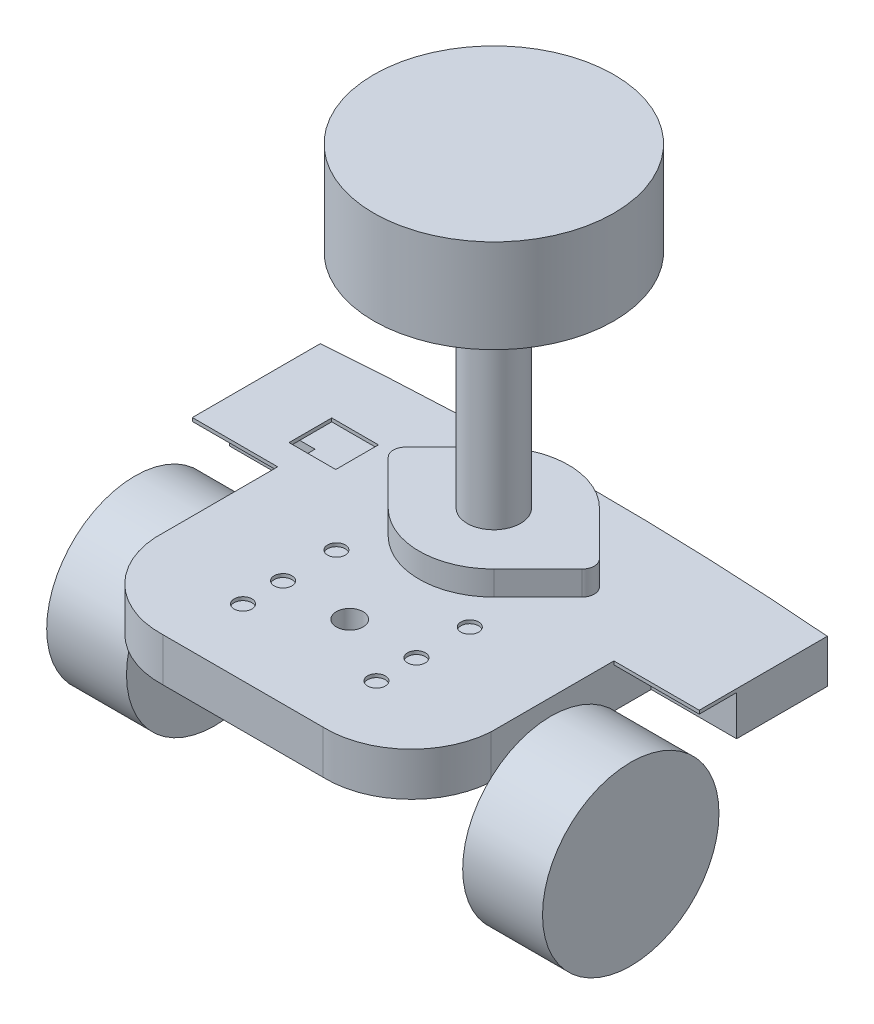
SolidWorks part; units mm, degrees
ref_plane "Front Plane" through (0, 0, 0) normal (0, 0, 1) x (1, 0, 0)
ref_plane "Top Plane" through (0, 0, 0) normal (0, 1, 0) x (1, 0, 0)
ref_plane "Right Plane" through (0, 0, 0) normal (1, 0, 0) x (0, 0, -1)
sketch "Sketch1" plane through (0, 0, 0) normal (0, 1, 0) x (1, 0, 0)
  line L0 (0, 0) -> (0, 125.2845) construction
  line L1 (19.05, 0) -> (-19.05, 0)
  line L2 (-40.005, 19.05) -> (-40.005, 48.26)
  line L3 (-40.005, 48.26) -> (-60.325, 48.26)
  line L4 (-60.325, 48.26) -> (-60.325, 78.74)
  line L5 (-60.325, 78.74) -> (60.325, 78.74)
  line L6 (60.325, 48.26) -> (60.325, 78.74)
  line L7 (40.005, 48.26) -> (60.325, 48.26)
  line L8 (40.005, 19.05) -> (40.005, 48.26)
  arc A0 (-40.005, 19.05) -> (-19.05, 0) centre (-19.724, 20.3088) ccw
  arc A1 (40.005, 19.05) -> (19.05, 0) centre (19.724, 20.3088) cw
  point P14 (0, 78.74)
  dimension "D4" = 20.32
  dimension "D1" = 120.65
  dimension "D2" = 80.01
  dimension "D3" = 38.1
  dimension "D5" = 19.05
  dimension "D6" = 48.26
  dimension "D7" = 78.74
extrude "Extrude1" add sketch "Sketch1" along normal blind 0.8128
sketch "Sketch3" plane through (0, 0.8128, 0) normal (0, 1, 0) x (-1, 0, 0)
  line L0 (0, -78.74) -> (0, 0) construction
  line L1 (-60.325, -78.74) -> (60.325, -78.74) construction
  line L2 (-21, -59.69) -> (21, -59.69) construction
  circle A0 centre (0, -59.69) radius 17.78
  circle A1 centre (21, -59.69) radius 1.651
  circle A2 centre (-21, -59.69) radius 1.651
  dimension "D1" = 35.56
  dimension "D3" = 42
  dimension "D4" = 3.302
  dimension "D2" = 19.05
extrude "Extrude2" cut sketch "Sketch3" against normal through all
sketch "Sketch4" plane through (0, 0.8128, 0) normal (0, 1, 0) x (-1, 0, 0)
  line L0 (38.1, -78.74) -> (38.1, -47.0431) construction
  line L1 (-60.325, -78.74) -> (60.325, -78.74) construction
  line L2 (60.325, -78.74) -> (60.325, -48.26) construction
  line L3 (38.1, -59.69) -> (21, -59.69) construction
  line L4 (43.6562, -54.61) -> (32.5438, -54.61)
  line L5 (43.6562, -54.61) -> (43.6562, -64.77)
  line L6 (43.6562, -64.77) -> (32.5438, -64.77)
  line L7 (32.5438, -54.61) -> (32.5438, -64.77)
  line L8 (43.6562, -54.61) -> (32.5438, -64.77) construction
  line L9 (43.6562, -64.77) -> (32.5438, -54.61) construction
  point P6 (38.1, -59.69)
  dimension "D1" = 22.225
  dimension "D2" = 11.1125
  dimension "D3" = 10.16
extrude "Cut-Extrude1" cut sketch "Sketch4" against normal through all
sketch "Sketch5" plane through (0, 0.8128, 0) normal (0, 1, 0) x (-1, 0, 0)
  line L0 (15.875, -78.74) -> (15.875, 0) construction
  line L1 (0, -78.74) -> (0, 0) construction
  line L2 (-60.325, -78.74) -> (60.325, -78.74) construction
  line L3 (19.05, 0) -> (-19.05, 0) construction
  circle A0 centre (15.875, -38.1) radius 2.1082
  circle A1 centre (15.875, -25.4) radius 2.1082
  circle A2 centre (15.875, -15.875) radius 2.1082
  circle A3 centre (-15.875, -15.875) radius 2.1082
  circle A4 centre (-15.875, -25.4) radius 2.1082
  circle A5 centre (-15.875, -38.1) radius 2.1082
  dimension "D2" = 4.2164
  dimension "D3" = 12.7
  dimension "D4" = 9.525
  dimension "D5" = 15.875
  dimension "D1" = 15.875
extrude "Extrude3" cut sketch "Sketch5" against normal through all
sketch "Sketch6" plane through (0, 0.8128, 0) normal (0, 1, 0) x (1, 0, 0)
  line L0 (-60.325, 78.74) -> (60.325, 78.74)
  arc A0 (-60.325, 78.74) -> (60.325, 78.74) centre (0, -680.8684) cw
  dimension "D1" = 762
extrude "Extrude5" add sketch "Sketch6" against normal through all
sketch "Sketch7" plane through (0, 0, 0) normal (0, -1, 0) x (1, 0, 0)
  line L7 (-60.325, -78.74) -> (-60.325, -57.15)
  line L8 (-60.325, -78.74) -> (-60.325, -48.26) construction
  line L9 (-60.325, -57.15) -> (-40.005, -57.15)
  line L10 (-60.325, -48.26) -> (-40.005, -48.26) construction
  line L11 (0, -81.1316) -> (0, 0) construction
  line L12 (60.325, -57.15) -> (40.005, -57.15)
  line L13 (60.325, -78.74) -> (60.325, -57.15)
  line L14 (-40.005, -19.05) -> (-40.005, -48.26)
  line L15 (-40.005, -48.26) -> (-60.325, -48.26)
  line L16 (-60.325, -48.26) -> (-60.325, -78.74)
  line L17 (60.325, -78.74) -> (60.325, -48.26)
  line L18 (60.325, -48.26) -> (40.005, -48.26)
  line L19 (40.005, -48.26) -> (40.005, -19.05)
  line L20 (19.05, 0) -> (-19.05, 0)
  line L21 (-40.005, -19.05) -> (-40.005, -57.15)
  line L26 (40.005, -57.15) -> (40.005, -19.05)
  line L27 (19.05, 0) -> (-19.05, 0)
  arc A6 (-19.05, 0) -> (-40.005, -19.05) centre (-19.724, -20.3088) ccw
  arc A7 (-60.325, -78.74) -> (60.325, -78.74) centre (0, 680.8684) ccw
  arc A8 (40.005, -19.05) -> (19.05, 0) centre (19.724, -20.3088) ccw
  arc A9 (-19.05, 0) -> (-40.005, -19.05) centre (-19.724, -20.3088) ccw
  arc A10 (-60.325, -78.74) -> (60.325, -78.74) centre (0, 680.8684) ccw
  arc A11 (40.005, -19.05) -> (19.05, 0) centre (19.724, -20.3088) ccw
  dimension "D2" = 8.89
  dimension "D1" = 0
extrude "Extrude6" add sketch "Sketch7" along normal blind 9.525
sketch "Sketch8" plane through (0, 0, 0) normal (0, 1, 0) x (1, 0, 0)
  line L0 (-23.0656, 61.7523) -> (-12.5824, 72.2523)
  line L1 (-21, 59.69) -> (0, 59.69) construction
  line L2 (0, 59.69) -> (0, 77.47) construction
  line L3 (23.0656, 61.7523) -> (12.5824, 72.2523)
  line L4 (-23.0656, 57.6277) -> (-12.5824, 47.1277)
  line L5 (23.0656, 57.6277) -> (12.5824, 47.1277)
  circle A0 centre (0, 59.69) radius 17.78
  circle A1 centre (21, 59.69) radius 2.9188
  circle A2 centre (-21, 59.69) radius 2.9188
  circle A3 centre (0, 59.69) radius 17.78 construction
  circle M1 centre (0, 59.69) radius 17.78
extrude "Extrude7" add sketch "Sketch8" along normal blind 6.604 contours A2 L4 L0 M1 | A2 | M1 | A1 L3 L5 M1 | A1
sketch "Sketch9" plane through (40.005, 0, 0) normal (1, 0, 0) x (0, 0, -1)
  line L0 (0, 0.8128) -> (0, -9.525) construction
  line L1 (19.05, 0.8128) -> (48.26, 0.8128) construction
  circle A0 centre (33.274, -24.0792) radius 21
  point P2 (0, -4.3561)
  dimension "D1" = 42
  dimension "D2" = 33.274
  dimension "D3" = 24.892
extrude "Extrude8" add sketch "Sketch9" along normal blind 19 separate body
mirror "Mirror3" about plane through (0, 0, 0) normal (1, 0, 0) of bodies 108
sketch "Sketch10" plane through (0, 6.604, 0) normal (0, 1, 0) x (-1, 0, 0)
  circle A0 centre (0, -59.69) radius 6.35
  dimension "D1" = 12.7
extrude "Extrude9" add sketch "Sketch10" along normal blind 52.832
sketch "Sketch11" plane through (0, 59.436, 0) normal (0, 1, 0) x (-1, 0, 0)
  circle A0 centre (0, -59.69) radius 28.575
  dimension "D1" = 57.15
extrude "Extrude10" add sketch "Sketch11" along normal blind 22.225 separate body
sketch "Sketch12" plane through (0, 0.8128, 0) normal (0, 1, 0) x (-1, 0, 0)
  line L0 (15.875, -25.4) -> (-15.875, -25.4) construction
  circle A0 centre (0, -25.4) radius 3.175
  dimension "D1" = 6.35
extrude "Extrude11" cut sketch "Sketch12" against normal through all
